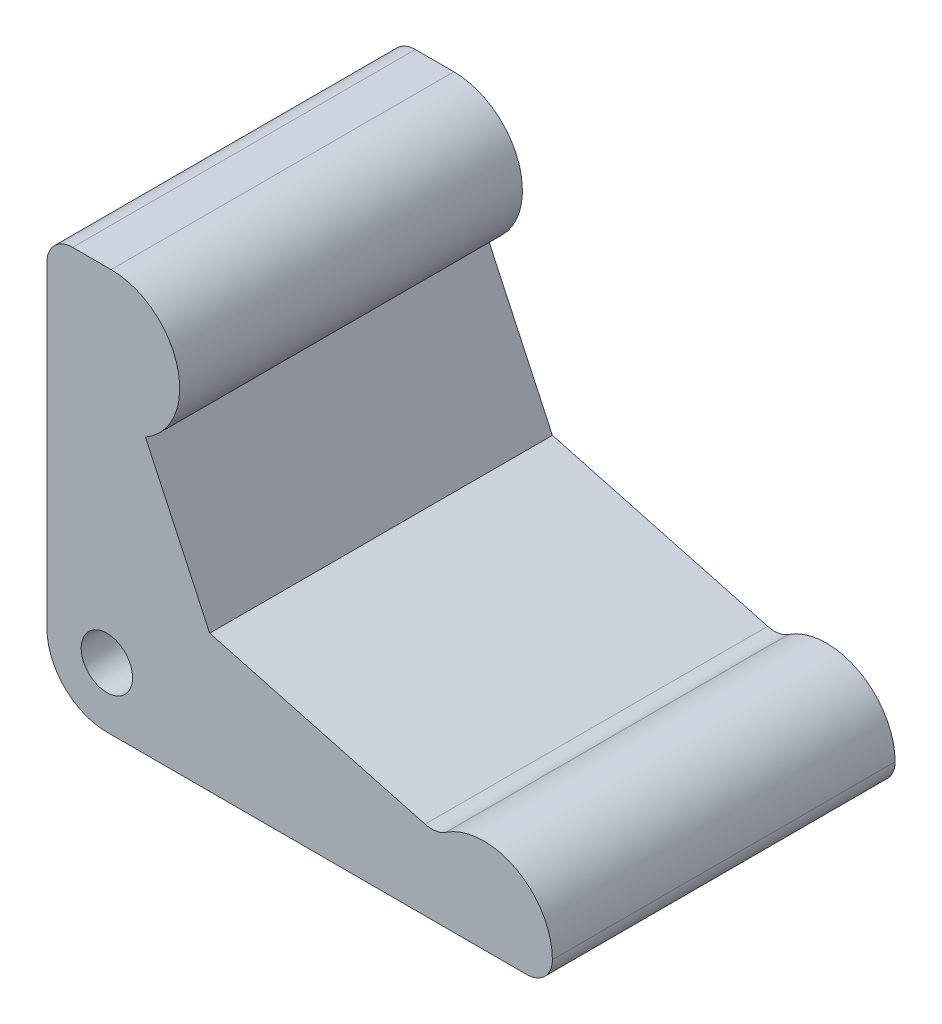
SolidWorks part; units mm, degrees
ref_plane "정면" through (0, 0, 0) normal (0, 0, 1) x (1, 0, 0)
ref_plane "윗면" through (0, 0, 0) normal (0, 1, 0) x (1, 0, 0)
ref_plane "우측면" through (0, 0, 0) normal (1, 0, 0) x (0, 0, -1)
sketch "스케치1" plane through (0, 0, 0) normal (0, 0, 1) x (1, 0, 0)
  line L0 (0, 7) -> (0, 44)
  line L1 (3, 47) -> (7.5, 47)
  line L2 (11.5044, 32.0743) -> (19, 16)
  line L3 (19, 16) -> (44.1367, 9.2646)
  line L4 (7, 0) -> (56, 0)
  line L5 (15.5, 61.2741) -> (15.5, -21.237) construction
  line L6 (40.4366, 11) -> (90.744, 11) construction
  line L7 (59, 54.6593) -> (59, -37.0778) construction
  arc A0 (7.5, 47) -> (11.5044, 32.0743) centre (7.5, 39) cw
  arc A1 (46.5732, 9.6636) -> (59, 3) centre (51, 3) cw
  arc A2 (56, 0) -> (59, 3) centre (56, 3) ccw
  arc A3 (46.5732, 9.6636) -> (44.1367, 9.2646) centre (44.9131, 12.1624) cw
  arc A4 (3, 47) -> (0, 44) centre (3, 44) ccw
  arc A5 (7, 0) -> (0, 7) centre (7, 7) cw
  circle A6 centre (7, 7) radius 3
  point P22 (0, 47)
  point P25 (0, 0)
  dimension "D2" = 130
  dimension "D4" = 8
  dimension "D8" = 8
  dimension "D9" = 11
  dimension "D11" = 3
  dimension "D12" = 7
  dimension "D13" = 6
  dimension "D1" = 47
  dimension "D3" = 16
  dimension "D5" = 19
  dimension "D6" = 15.5
  dimension "D7" = 65
  dimension "D10" = 59
extrude "보스-돌출1" add sketch "스케치1" along normal mid plane 40
sketch "스케치2" plane through (0, 0, 0) normal (0, -1, 0) x (1, 0, 0)
  line L0 (0, 20) -> (0, -20) construction
  circle A0 centre (49, 0) radius 7
  dimension "D2" = 14
  dimension "D1" = 49
extrude "컷-돌출1" cut sketch "스케치2" against normal blind 4
